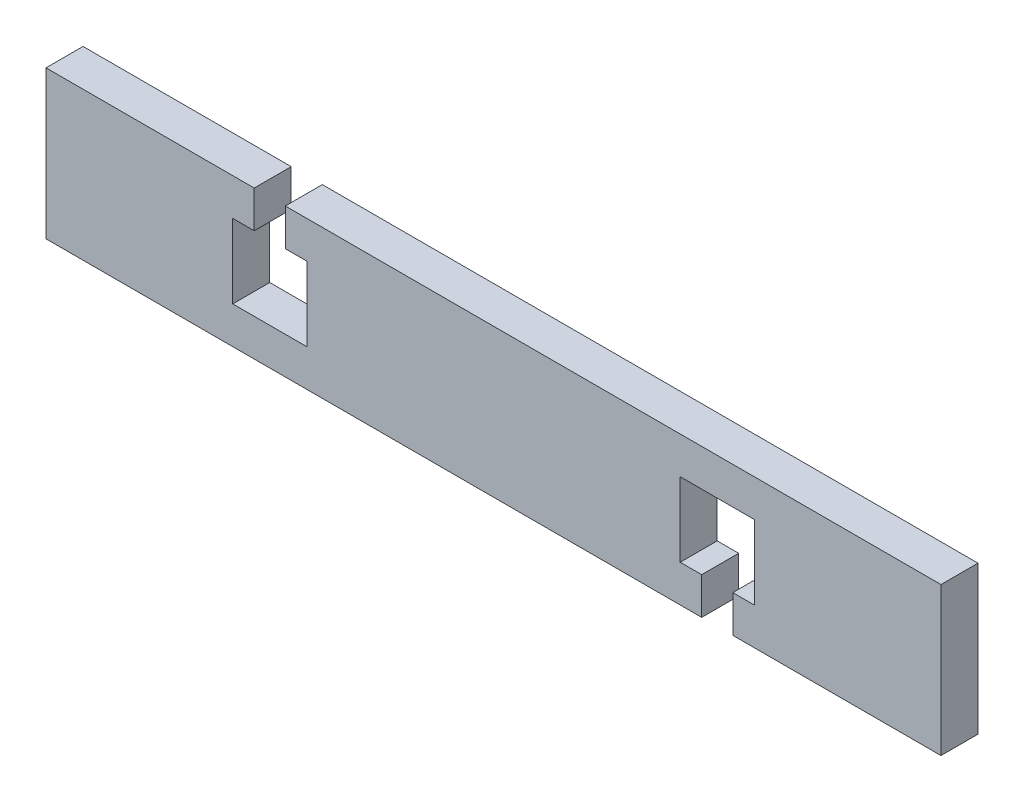
SolidWorks part; units mm, degrees
ref_plane "Front Plane" through (0, 0, 0) normal (0, 0, 1) x (1, 0, 0)
ref_plane "Top Plane" through (0, 0, 0) normal (0, 1, 0) x (1, 0, 0)
ref_plane "Right Plane" through (0, 0, 0) normal (1, 0, 0) x (0, 0, -1)
sketch "Sketch1" plane through (0, 0, 0) normal (0, 0, 1) x (1, 0, 0)
  line L0 (0, 10) -> (0, -6.0965) construction
  line L1 (60.425, -10) -> (32.3125, -10)
  line L2 (60.425, -10) -> (60.425, 10)
  line L3 (60.425, 10) -> (-28.1125, 10)
  line L4 (-60.425, -10) -> (-60.425, 10)
  line L5 (60.425, -10) -> (-60.425, 10) construction
  line L6 (60.425, 10) -> (-60.425, -10) construction
  line L7 (0, -6.0965) -> (-60.425, -6.0965) construction
  line L8 (-30.2125, -6.0965) -> (-30.2125, 10) construction
  line L9 (60.425, 5.2934) -> (0, 5.2934) construction
  line L10 (0, -10) -> (0, 5.2934) construction
  line L11 (30.2125, 5.2934) -> (30.2125, -10) construction
  line L12 (-32.3125, 10) -> (-32.3125, 5)
  line L13 (-32.3125, 5) -> (-35.2125, 5)
  line L14 (-35.2125, 5) -> (-35.2125, -5)
  line L15 (-35.2125, -5) -> (-30.2125, -5)
  line L16 (-25.2125, -5) -> (-30.2125, -5)
  line L17 (-25.2125, 5) -> (-25.2125, -5)
  line L18 (-28.1125, 5) -> (-25.2125, 5)
  line L19 (-28.1125, 10) -> (-28.1125, 5)
  line L20 (-32.3125, 10) -> (-60.425, 10)
  line L21 (28.1125, -10) -> (28.1125, -5)
  line L22 (28.1125, -5) -> (25.2125, -5)
  line L23 (25.2125, -5) -> (25.2125, 5)
  line L24 (25.2125, 5) -> (35.2125, 5)
  line L25 (32.3125, -10) -> (32.3125, -5)
  line L26 (32.3125, -5) -> (35.2125, -5)
  line L27 (35.2125, -5) -> (35.2125, 5)
  line L28 (28.1125, -10) -> (-60.425, -10)
  point P0 (0, 0)
  point P34 (30.2125, 5)
  dimension "D1" = 120.85
  dimension "D2" = 20
  dimension "D3" = 2.1
  dimension "D4" = 5
  dimension "D5" = 5
  dimension "D6" = 10
  dimension "D7" = 2.1
  dimension "D8" = 5
  dimension "D9" = 10
  dimension "D10" = 5
extrude "Boss-Extrude1" add sketch "Sketch1" along normal blind 5
